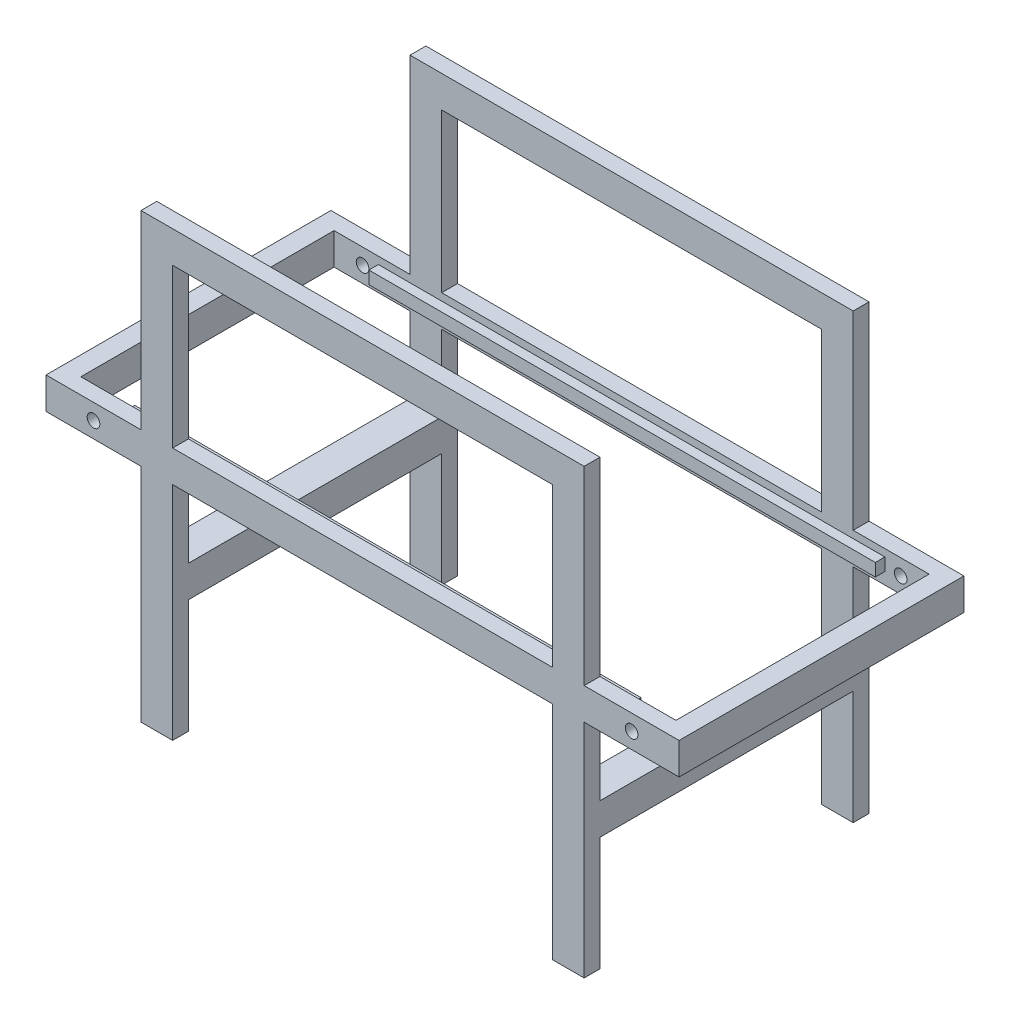
SolidWorks part; units mm, degrees
ref_plane "Alzado" through (0, 0, 0) normal (0, 0, 1) x (1, 0, 0)
ref_plane "Planta" through (0, 0, 0) normal (0, 1, 0) x (1, 0, 0)
ref_plane "Vista lateral" through (0, 0, 0) normal (1, 0, 0) x (0, 0, -1)
sketch "Croquis1" plane through (0, 0, 0) normal (0, 0, 1) x (1, 0, 0)
  line L0 (-500, 0) -> (500, 0) construction
  line L1 (0, 50) -> (0, 0) construction
  line L2 (-500, 0) -> (500, 0)
  line L3 (-500, 0) -> (-500, 50)
  line L4 (-500, 50) -> (500, 50)
  line L5 (500, 0) -> (500, 50)
  line L6 (-350, 350) -> (350, 350)
  line L7 (-350, 350) -> (-350, 300)
  line L8 (-350, 300) -> (350, 300)
  line L9 (350, 350) -> (350, 300)
  line L10 (-350, 300) -> (-300, 300)
  line L11 (-350, 300) -> (-350, 50)
  line L12 (-350, 50) -> (-300, 50)
  line L13 (-300, 300) -> (-300, 50)
  line L14 (300, 300) -> (350, 300)
  line L15 (300, 300) -> (300, 50)
  line L16 (300, 50) -> (350, 50)
  line L17 (350, 300) -> (350, 50)
  line L18 (-350, 0) -> (-300, 0)
  line L19 (-350, 0) -> (-350, -350)
  line L20 (-350, -350) -> (-300, -350)
  line L21 (-300, 0) -> (-300, -350)
  line L22 (300, 0) -> (350, 0)
  line L23 (300, 0) -> (300, -350)
  line L24 (300, -350) -> (350, -350)
  line L25 (350, 0) -> (350, -350)
  line L26 (-425, 25) -> (425, 25) construction
  circle A0 centre (-425, 25) radius 10
  circle A5 centre (425, 25) radius 10
  point P4 (0, 0)
  point P28 (500, 25)
  point P34 (0, 25)
  dimension "D12" = 20
  dimension "D1" = 50
  dimension "D2" = 50
  dimension "D3" = 1000
  dimension "D4" = 150
  dimension "D5" = 150
  dimension "D6" = 150
  dimension "D7" = 50
  dimension "D8" = 150
  dimension "D9" = 250
  dimension "D10" = 350
  dimension "D11" = 850
extrude "Saliente-Extruir1" add sketch "Croquis1" along normal blind 450
sketch "Croquis4" plane through (-350, 0, 0) normal (-1, 0, 0) x (0, 0, 1)
  line L0 (450, 350) -> (0, 350) construction
  line L1 (25, 350) -> (425, 350)
  line L2 (25, 350) -> (25, -120)
  line L3 (25, -120) -> (425, -120)
  line L4 (425, 350) -> (425, -120)
  line L5 (450, -350) -> (0, -350) construction
  line L6 (25, -170) -> (425, -170)
  line L7 (25, -170) -> (25, -350)
  line L8 (25, -350) -> (425, -350)
  line L9 (425, -170) -> (425, -350)
  line L10 (0, 0) -> (0, -350) construction
  line L11 (450, 350) -> (450, 50) construction
  line L12 (450, 0) -> (450, -350) construction
  dimension "D1" = 50
  dimension "D2" = 25
  dimension "D3" = 180
  dimension "D4" = 25
  dimension "D5" = 25
  dimension "D6" = 25
extrude "Cortar-Extruir1" cut sketch "Croquis4" along normal through all and the other way through all
sketch "Croquis5" plane through (0, 0, 450) normal (0, 0, 1) x (1, 0, 0)
  line L1 (-500, 50) -> (-470, 50)
  line L2 (-500, 50) -> (-500, 0)
  line L3 (-500, 0) -> (-470, 0)
  line L4 (-470, 50) -> (-470, 0)
  line L5 (-500, 0) -> (-350, 0) construction
  line L7 (500, 50) -> (470, 50)
  line L8 (500, 50) -> (500, 0)
  line L9 (500, 0) -> (470, 0)
  line L10 (470, 50) -> (470, 0)
  line L11 (350, 0) -> (500, 0) construction
  dimension "D1" = 50
  dimension "D2" = 30
  dimension "D3" = 50
  dimension "D4" = 30
extrude "Saliente-Extruir2" add sketch "Croquis5" against normal up to surface (425 mm away) up to face at (425, 15, 25)
sketch "Croquis6" plane through (0, 0, 0) normal (1, 0, 0) x (0, 0, -1)
  line L0 (-25, 18.5) -> (-40, 18.5)
  line L1 (-425, 38.5) -> (-410, 38.5)
  line L2 (-425, 38.5) -> (-425, 18.5)
  line L3 (-425, 18.5) -> (-410, 18.5)
  line L4 (-410, 38.5) -> (-410, 18.5)
  line L5 (-450, 50) -> (0, 50) construction
  line L6 (-425, 15) -> (-425, 35) construction
  line L7 (-225, 38.5) -> (-225, 154.0963) construction
  line L8 (-425, 38.5) -> (-25, 38.5) construction
  line L9 (-40, 38.5) -> (-40, 18.5)
  line L10 (-25, 38.5) -> (-40, 38.5)
  line L11 (-25, 38.5) -> (-25, 18.5)
  point P12 (-225, 38.5)
  dimension "D1" = 20
  dimension "D2" = 15
  dimension "D3" = 11.5
  dimension "D4" = 0
  dimension "D5" = 400
extrude "Saliente-Extruir3" add sketch "Croquis6" along normal blind 400 and the other way blind 400
